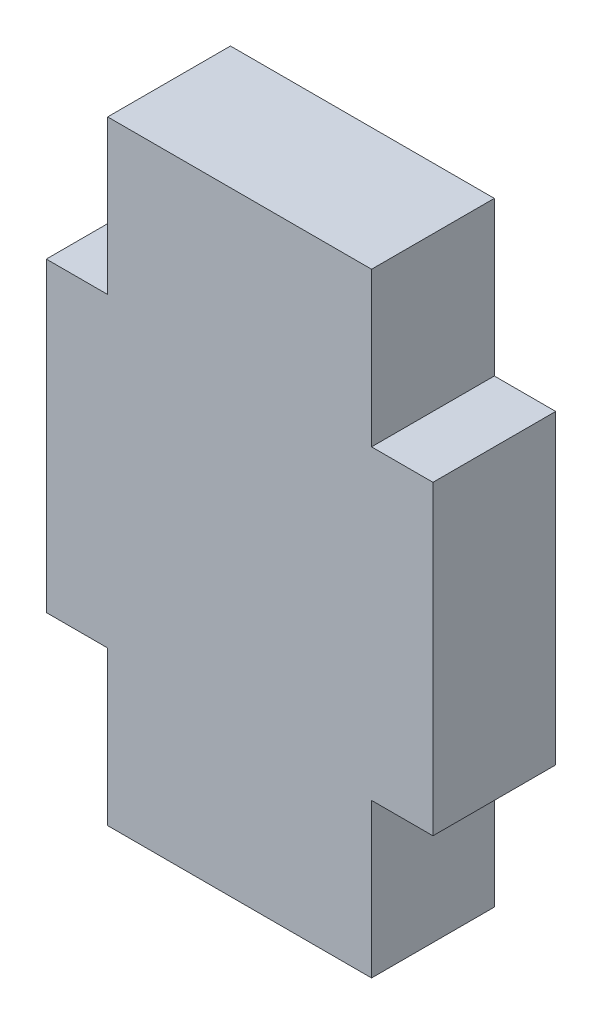
SolidWorks part; units mm, degrees
ref_plane "Front Plane" through (0, 0, 0) normal (0, 0, 1) x (1, 0, 0)
ref_plane "Top Plane" through (0, 0, 0) normal (0, 1, 0) x (1, 0, 0)
ref_plane "Right Plane" through (0, 0, 0) normal (1, 0, 0) x (0, 0, -1)
sketch "Sketch1" plane through (0, 0, 0) normal (0, 0, 1) x (1, 0, 0)
  line L0 (-12.064, 73.6415) -> (-12.064, 99.0415) construction
  line L1 (-20.064, 86.3415) -> (-4.064, 86.3415) construction
  line L12 (-17.524, 73.6415) -> (-6.604, 73.6415)
  line L13 (-17.524, 80.0071) -> (-17.524, 73.6415)
  line L14 (-6.604, 73.6415) -> (-6.604, 80.0071)
  line L15 (-6.604, 80.0071) -> (-4.064, 80.0071)
  line L16 (-4.064, 80.0071) -> (-4.064, 92.6759)
  line L17 (-6.604, 92.6759) -> (-4.064, 92.6759)
  line L18 (-6.604, 92.6759) -> (-6.604, 99.0415)
  line L19 (-17.524, 99.0415) -> (-6.604, 99.0415)
  line L20 (-17.524, 99.0415) -> (-17.524, 92.6759)
  line L21 (-17.524, 92.6759) -> (-20.064, 92.6759)
  line L22 (-20.064, 92.6759) -> (-20.064, 80.0071)
  line L23 (-17.524, 80.0071) -> (-20.064, 80.0071)
  point P16 (-12.064, 86.3415)
  dimension "D1" = 25.4
  dimension "D2" = 5.46
extrude "Boss-Extrude1" add sketch "Sketch1" along normal blind 5.08
